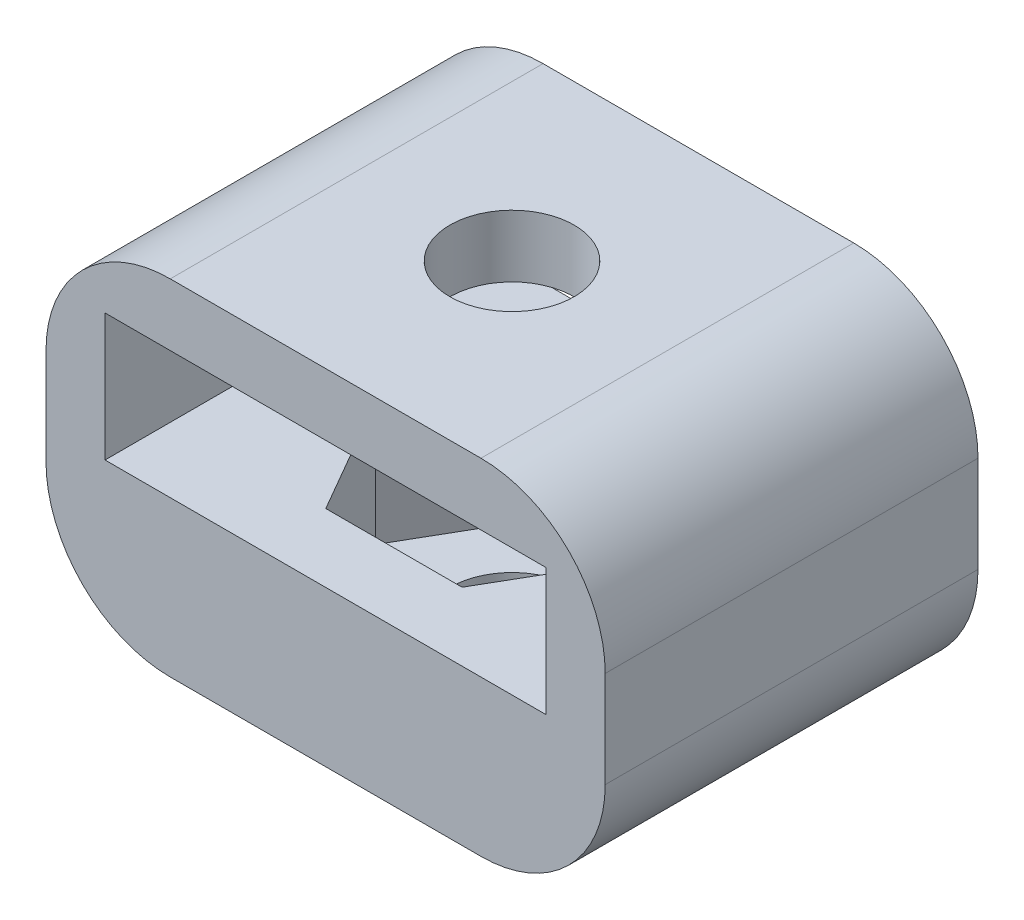
SolidWorks part; units mm, degrees
material "3D printer PLA"
ref_plane "Front Plane" through (0, 0, 0) normal (0, 0, 1) x (1, 0, 0)
ref_plane "Top Plane" through (0, 0, 0) normal (0, 1, 0) x (1, 0, 0)
ref_plane "Right Plane" through (0, 0, 0) normal (1, 0, 0) x (0, 0, -1)
sketch "Sketch1" plane through (0, 0, 0) normal (0, 1, 0) x (1, 0, 0)
  line L1 (-11.43, 7.62) -> (11.43, 7.62)
  line L2 (-11.43, 7.62) -> (-11.43, -7.62)
  line L3 (-11.43, -7.62) -> (11.43, -7.62)
  line L4 (11.43, 7.62) -> (11.43, -7.62)
  line L5 (-11.43, 7.62) -> (11.43, -7.62) construction
  line L6 (-11.43, -7.62) -> (11.43, 7.62) construction
  line L7 (5.5726, 0) -> (2.7863, 4.826)
  line L8 (2.7863, 4.826) -> (-2.7863, 4.826)
  line L9 (-2.7863, 4.826) -> (-5.5726, 0)
  line L10 (-5.5726, 0) -> (-2.7863, -4.826)
  line L11 (-2.7863, -4.826) -> (2.7863, -4.826)
  line L12 (2.7863, -4.826) -> (5.5726, 0)
  circle A0 centre (0, 0) radius 4.826 construction
  point P0 (0, 0)
  dimension "D1" = 9.652
  dimension "D2" = 22.86
  dimension "D3" = 15.24
extrude "Boss-Extrude1" add sketch "Sketch1" along normal blind 5.08
sketch "Sketch3" plane through (0, 5.08, 0) normal (0, 1, 0) x (1, 0, 0)
  line L0 (-11.43, -7.62) -> (11.43, -7.62) construction
  line L1 (-11.43, 7.62) -> (-9.017, 7.62)
  line L2 (-11.43, 7.62) -> (-11.43, -7.62)
  line L3 (-11.43, -7.62) -> (-9.017, -7.62)
  line L4 (-9.017, 7.62) -> (-9.017, -7.62)
  line L5 (-11.43, 7.62) -> (-9.017, -7.62) construction
  line L6 (-11.43, -7.62) -> (-9.017, 7.62) construction
  line L8 (11.43, 7.62) -> (9.017, 7.62)
  line L9 (11.43, 7.62) -> (11.43, -7.62)
  line L10 (11.43, -7.62) -> (9.017, -7.62)
  line L11 (9.017, 7.62) -> (9.017, -7.62)
  line L12 (11.43, 7.62) -> (9.017, -7.62) construction
  line L13 (11.43, -7.62) -> (9.017, 7.62) construction
  point P4 (-10.2235, 0)
  point P12 (10.2235, 0)
  dimension "D1" = 2.413
  dimension "D2" = 2.413
extrude "Boss-Extrude3" add sketch "Sketch3" along normal blind 5.207
sketch "Sketch4" plane through (0, 10.287, 0) normal (0, 1, 0) x (1, 0, 0)
  line L1 (-11.43, 7.62) -> (11.43, 7.62)
  line L2 (-11.43, 7.62) -> (-11.43, -7.62)
  line L3 (-11.43, -7.62) -> (11.43, -7.62)
  line L4 (11.43, 7.62) -> (11.43, -7.62)
  line L5 (-11.43, 7.62) -> (11.43, -7.62) construction
  line L6 (-11.43, -7.62) -> (11.43, 7.62) construction
  circle A0 centre (0, 0) radius 2.54
  point P4 (0, 0)
  dimension "D1" = 5.08
extrude "Boss-Extrude4" add sketch "Sketch4" along normal blind 2.54
sketch "Sketch5" plane through (0, 0, 0) normal (0, -1, 0) x (1, 0, 0)
  line L1 (-11.43, 7.62) -> (11.43, 7.62)
  line L2 (-11.43, 7.62) -> (-11.43, -7.62)
  line L3 (-11.43, -7.62) -> (11.43, -7.62)
  line L4 (11.43, 7.62) -> (11.43, -7.62)
  line L5 (-11.43, 7.62) -> (11.43, -7.62) construction
  line L6 (-11.43, -7.62) -> (11.43, 7.62) construction
  circle A0 centre (0, 0) radius 2.54
  point P4 (0, 0)
extrude "Boss-Extrude5" add sketch "Sketch5" along normal blind 1.27
fillet "Fillet1" radius 5.08 4 edges at (11.43, 12.827, 0) (11.43, -1.27, 0) (-11.43, -1.27, 0) (-11.43, 12.827, 0)
